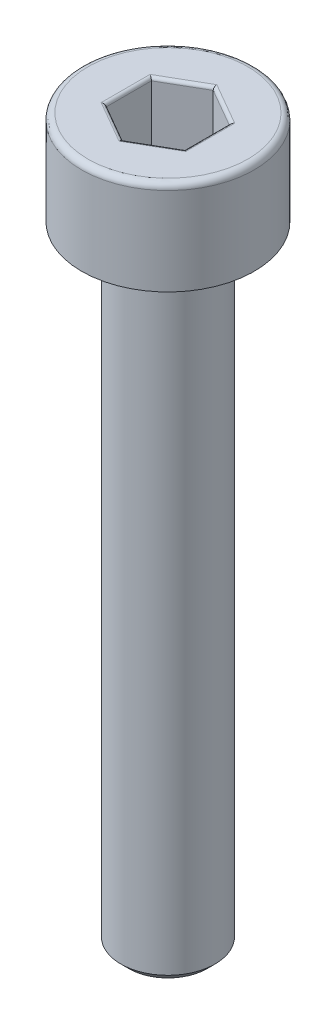
SolidWorks part; units mm, degrees
ref_plane "Front Plane" through (0, 0, 0) normal (0, 0, 1) x (1, 0, 0)
ref_plane "Top Plane" through (0, 0, 0) normal (0, 1, 0) x (1, 0, 0)
ref_plane "Right Plane" through (0, 0, 0) normal (1, 0, 0) x (0, 0, -1)
sketch "Sketch1" plane through (0, 0, 0) normal (0, 0, 1) x (1, 0, 0)
  line L0 (0, 0) -> (0, -47.0967) construction
  line L1 (0, -23) -> (-1.5, -23)
  line L2 (-1.5, -23) -> (-1.5, -3)
  line L3 (-1.5, -3) -> (-2.75, -3)
  line L4 (-2.75, -3) -> (-2.75, 0)
  line L5 (-2.75, 0) -> (0, 0)
  line L6 (0, 0) -> (0, -23)
  dimension "D1" = 20
  dimension "d" = 3
  dimension "k" = 3
  dimension "dk" = 5.5
revolve "Revolve1" add sketch "Sketch1" angle 360 about L0
chamfer "Chamfer1" distance 0.25 angle 45 2 edges at (0, -3, 1.5) (0, -23, 1.5)
fillet "Fillet1" radius 0.2 1 edges at (0, 0, 2.75)
sketch "Sketch2" plane through (0, 0, 0) normal (0, 1, 0) x (1, 0, 0)
  line L1 (0, 1.4434) -> (-1.25, 0.7217)
  line L2 (-1.25, 0.7217) -> (-1.25, -0.7217)
  line L3 (-1.25, -0.7217) -> (0, -1.4434)
  line L4 (0, -1.4434) -> (1.25, -0.7217)
  line L5 (1.25, -0.7217) -> (1.25, 0.7217)
  line L6 (1.25, 0.7217) -> (0, 1.4434)
  circle A0 centre (0, 0) radius 1.25 construction
  dimension "s" = 2.5
extrude "Cut-Extrude1" cut sketch "Sketch2" against normal blind 2
fillet "Fillet2" radius 0.1 12 edges at (-0.625, 0, -1.0825) (-1.25, 0, 0) (-0.625, 0, 1.0825) (0.625, 0, 1.0825) (1.25, 0, 0) (0.625, 0, -1.0825) (1.25, -2, 0) (0.625, -2, 1.0825) (-0.625, -2, 1.0825) (-1.25, -2, 0) (-0.625, -2, -1.0825) (0.625, -2, -1.0825)
